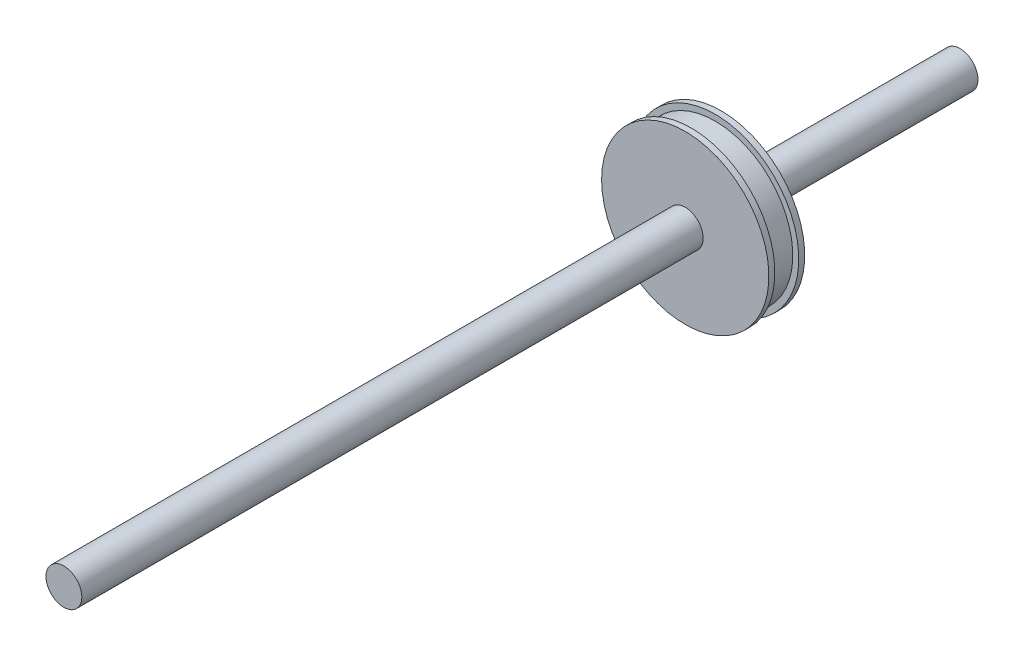
SolidWorks part; units mm, degrees
ref_plane "Front Plane" through (0, 0, 0) normal (0, 0, 1) x (1, 0, 0)
ref_plane "Top Plane" through (0, 0, 0) normal (0, 1, 0) x (1, 0, 0)
ref_plane "Right Plane" through (0, 0, 0) normal (1, 0, 0) x (0, 0, -1)
sketch "Sketch1" plane through (0, 0, 0) normal (0, 0, 1) x (1, 0, 0)
  circle A0 centre (0, 0) radius 1.5
  dimension "D1" = 3
extrude "Boss-Extrude1" add sketch "Sketch1" along normal blind 75
sketch "Sketch2" plane through (0, 0, 0) normal (0, 1, 0) x (1, 0, 0)
  line L0 (7, -20) -> (7, -20.5)
  line L1 (0, -20) -> (7, -20)
  line L2 (0, -20) -> (0, -23)
  line L3 (0, -23) -> (7, -23)
  line L5 (1.5, 0) -> (-1.5, 0) construction
  line L6 (6.5, -21.5) -> (0, -21.5) construction
  line L7 (7, -20.5) -> (6.5, -20.5)
  line L8 (6.5, -20.5) -> (6.5, -22.5)
  line L9 (7, -22.5) -> (6.5, -22.5)
  line L10 (7, -22.5) -> (7, -23)
  point P13 (6.5, -21.5)
  point P14 (6.5, -21)
  dimension "D4" = 0.5
  dimension "D1" = 20
  dimension "D2" = 3
  dimension "D3" = 7
  dimension "D5" = 2
revolve "Revolve1" add sketch "Sketch2" angle 360 about L2
